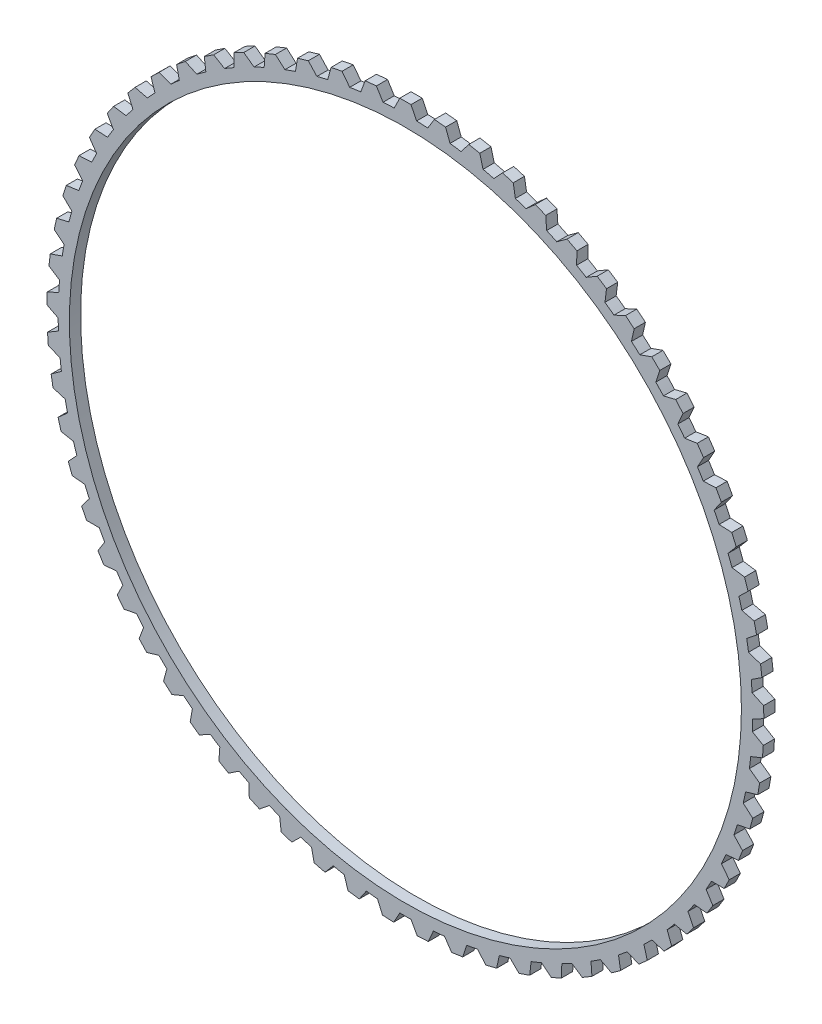
SolidWorks part; units mm, degrees
ref_plane "Front Plane" through (0, 0, 0) normal (0, 0, 1) x (1, 0, 0)
ref_plane "Top Plane" through (0, 0, 0) normal (0, 1, 0) x (1, 0, 0)
ref_plane "Right Plane" through (0, 0, 0) normal (1, 0, 0) x (0, 0, -1)
sketch "Sketch1" plane through (0, 0, 0) normal (0, 0, 1) x (1, 0, 0)
  line L0 (0, 320) -> (0, 310) construction
  line L1 (-5, 320) -> (5, 320)
  line L2 (-5, 320) -> (-9.9987, 309.8387)
  line L3 (5, 320) -> (9.9987, 309.8387)
  line L4 (25.9078, 318.9887) -> (35.8611, 318.0236)
  line L5 (35.8611, 318.0236) -> (39.8558, 307.4273)
  line L6 (25.9078, 318.9887) -> (19.9517, 309.3573)
  line L7 (56.5737, 314.9991) -> (66.3874, 313.0778)
  line L8 (66.3874, 313.0778) -> (69.3407, 302.1454)
  line L9 (56.5737, 314.9991) -> (49.7159, 305.9875)
  line L10 (86.7114, 308.0684) -> (96.2938, 305.2089)
  line L11 (96.2938, 305.2089) -> (98.1783, 294.0426)
  line L12 (86.7114, 308.0684) -> (79.0158, 299.7607)
  line L13 (116.0395, 298.2614) -> (125.3012, 294.4904)
  line L14 (125.3012, 294.4904) -> (126.0991, 283.1943)
  line L15 (116.0395, 298.2614) -> (107.578, 290.7352)
  line L16 (144.2841, 285.6695) -> (153.1387, 281.0223)
  line L17 (153.1387, 281.0223) -> (152.8426, 269.7019)
  line L18 (144.2841, 285.6695) -> (135.1358, 278.9952)
  line L19 (171.1817, 270.4105) -> (179.5464, 264.9304)
  line L20 (179.5464, 264.9304) -> (178.1591, 253.6914)
  line L21 (171.1817, 270.4105) -> (161.4319, 264.6502)
  line L22 (196.4809, 252.6267) -> (204.2776, 246.3649)
  line L23 (204.2776, 246.3649) -> (201.8121, 235.3123)
  line L24 (196.4809, 252.6267) -> (186.2207, 247.8343)
  line L25 (219.9456, 232.4842) -> (227.1016, 225.4991)
  line L26 (227.1016, 225.4991) -> (223.5809, 214.7361)
  line L27 (219.9456, 232.4842) -> (209.2708, 228.7045)
  line L28 (241.3568, 210.1711) -> (247.8052, 202.5279)
  line L29 (247.8052, 202.5279) -> (243.2622, 192.1549)
  line L30 (241.3568, 210.1711) -> (230.367, 207.4392)
  line L31 (260.5145, 185.8956) -> (266.1952, 177.6658)
  line L32 (266.1952, 177.6658) -> (260.6722, 167.7797)
  line L33 (260.5145, 185.8956) -> (249.3124, 184.2372)
  line L34 (277.2399, 159.8845) -> (282.0997, 151.1449)
  line L35 (282.0997, 151.1449) -> (275.6483, 141.8379)
  line L36 (277.2399, 159.8845) -> (265.9299, 159.315)
  line L37 (291.3767, 132.3806) -> (295.3703, 123.2127)
  line L38 (295.3703, 123.2127) -> (288.0508, 114.5719)
  line L39 (291.3767, 132.3806) -> (280.0646, 132.9053)
  line L40 (302.793, 103.6407) -> (305.8832, 94.1302)
  line L41 (305.8832, 94.1302) -> (297.7639, 86.2361)
  line L42 (302.793, 103.6407) -> (291.5844, 105.2548)
  line L43 (311.3822, 73.9331) -> (313.5401, 64.1687)
  line L44 (313.5401, 64.1687) -> (304.6968, 57.0952)
  line L45 (311.3822, 73.9331) -> (300.3817, 76.6214)
  line L46 (317.0642, 43.5353) -> (318.2695, 33.6082)
  line L47 (318.2695, 33.6082) -> (308.7848, 27.4211)
  line L48 (317.0642, 43.5353) -> (306.3744, 47.2727)
  line L49 (319.7857, 12.7309) -> (320.0274, 2.7339)
  line L50 (320.0274, 2.7339) -> (309.9898, -2.5089)
  line L51 (319.7857, 12.7309) -> (309.5066, 17.4826)
  line L52 (319.5216, -18.1923) -> (318.7972, -28.166)
  line L53 (318.7972, -28.166) -> (308.3006, -32.4155)
  line L54 (319.5216, -18.1923) -> (309.7491, -12.4707)
  line L55 (316.2741, -48.9456) -> (314.5906, -58.8029)
  line L56 (314.5906, -58.8029) -> (303.7327, -62.0195)
  line L57 (316.2741, -48.9456) -> (307.0994, -42.3075)
  line L58 (310.0737, -79.242) -> (307.4466, -88.8907)
  line L59 (307.4466, -88.8907) -> (296.3291, -91.0444)
  line L60 (310.0737, -79.242) -> (301.5825, -71.7494)
  line L61 (300.9782, -108.7985) -> (297.4322, -118.1486)
  line L62 (297.4322, -118.1486) -> (286.1586, -119.2193)
  line L63 (300.9782, -108.7985) -> (293.2498, -100.5214)
  line L64 (289.0726, -137.3392) -> (284.6407, -146.3034)
  line L65 (284.6407, -146.3034) -> (273.3164, -146.281)
  line L66 (289.0726, -137.3392) -> (282.1791, -128.3548)
  line L67 (274.4679, -164.5975) -> (269.1915, -173.0922)
  line L68 (269.1915, -173.0922) -> (257.9223, -171.9769)
  line L69 (274.4679, -164.5975) -> (268.4738, -154.9898)
  line L70 (257.3007, -190.3191) -> (251.229, -198.2649)
  line L71 (251.229, -198.2649) -> (240.1201, -196.0672)
  line L72 (257.3007, -190.3191) -> (252.2618, -180.1777)
  line L73 (237.7311, -214.2637) -> (230.9209, -221.5864)
  line L74 (230.9209, -221.5864) -> (220.0759, -218.3268)
  line L75 (237.7311, -214.2637) -> (233.6945, -203.6833)
  line L76 (215.9418, -236.2078) -> (208.4567, -242.8391)
  line L77 (208.4567, -242.8391) -> (197.9769, -238.548)
  line L78 (215.9418, -236.2078) -> (212.9452, -225.2872)
  line L79 (192.1364, -255.9465) -> (184.0462, -261.8244)
  line L80 (184.0462, -261.8244) -> (174.0295, -256.5419)
  line L81 (192.1364, -255.9465) -> (190.2077, -244.7877)
  line L82 (166.537, -273.2955) -> (157.9173, -278.3651)
  line L83 (157.9173, -278.3651) -> (148.4572, -272.1405)
  line L84 (166.537, -273.2955) -> (165.6944, -262.0026)
  line L85 (139.3827, -288.0928) -> (130.314, -292.3068)
  line L86 (130.314, -292.3068) -> (121.4988, -285.1982)
  line L87 (139.3827, -288.0928) -> (139.6339, -276.7713)
  line L88 (110.9271, -300.2002) -> (101.494, -303.5193)
  line L89 (101.494, -303.5193) -> (93.406, -295.5932)
  line L90 (110.9271, -300.2002) -> (112.2698, -288.9559)
  line L91 (81.4357, -309.5048) -> (71.7263, -311.898)
  line L92 (71.7263, -311.898) -> (64.4411, -303.2282)
  line L93 (81.4357, -309.5048) -> (83.8574, -298.4425)
  line L94 (51.184, -315.9196) -> (41.289, -317.3645)
  line L95 (41.289, -317.3645) -> (34.8745, -308.0321)
  line L96 (51.184, -315.9196) -> (54.6621, -305.1427)
  line L97 (20.4544, -319.3847) -> (10.4661, -319.8679)
  line L98 (10.4661, -319.8679) -> (4.9823, -309.96)
  line L99 (20.4544, -319.3847) -> (24.9564, -308.9938)
  line L100 (-10.4661, -319.8679) -> (-20.4544, -319.3847)
  line L101 (-20.4544, -319.3847) -> (-24.9564, -308.9938)
  line L102 (-10.4661, -319.8679) -> (-4.9823, -309.96)
  line L103 (-41.289, -317.3645) -> (-51.184, -315.9196)
  line L104 (-51.184, -315.9196) -> (-54.6621, -305.1427)
  line L105 (-41.289, -317.3645) -> (-34.8745, -308.0321)
  line L106 (-71.7263, -311.898) -> (-81.4357, -309.5048)
  line L107 (-81.4357, -309.5048) -> (-83.8574, -298.4425)
  line L108 (-71.7263, -311.898) -> (-64.4411, -303.2282)
  line L109 (-101.494, -303.5193) -> (-110.9271, -300.2002)
  line L110 (-110.9271, -300.2002) -> (-112.2698, -288.9559)
  line L111 (-101.494, -303.5193) -> (-93.406, -295.5932)
  line L112 (-130.314, -292.3068) -> (-139.3827, -288.0928)
  line L113 (-139.3827, -288.0928) -> (-139.6339, -276.7713)
  line L114 (-130.314, -292.3068) -> (-121.4988, -285.1982)
  line L115 (-157.9173, -278.3651) -> (-166.537, -273.2955)
  line L116 (-166.537, -273.2955) -> (-165.6944, -262.0026)
  line L117 (-157.9173, -278.3651) -> (-148.4572, -272.1405)
  line L118 (-184.0462, -261.8244) -> (-192.1364, -255.9465)
  line L119 (-192.1364, -255.9465) -> (-190.2077, -244.7877)
  line L120 (-184.0462, -261.8244) -> (-174.0295, -256.5419)
  line L121 (-208.4567, -242.8391) -> (-215.9418, -236.2078)
  line L122 (-215.9418, -236.2078) -> (-212.9452, -225.2872)
  line L123 (-208.4567, -242.8391) -> (-197.9769, -238.548)
  line L124 (-230.9209, -221.5864) -> (-237.7311, -214.2637)
  line L125 (-237.7311, -214.2637) -> (-233.6945, -203.6833)
  line L126 (-230.9209, -221.5864) -> (-220.0759, -218.3268)
  line L127 (-251.229, -198.2649) -> (-257.3007, -190.3191)
  line L128 (-257.3007, -190.3191) -> (-252.2618, -180.1777)
  line L129 (-251.229, -198.2649) -> (-240.1201, -196.0672)
  line L130 (-269.1915, -173.0922) -> (-274.4679, -164.5975)
  line L131 (-274.4679, -164.5975) -> (-268.4738, -154.9898)
  line L132 (-269.1915, -173.0922) -> (-257.9223, -171.9769)
  line L133 (-284.6407, -146.3034) -> (-289.0726, -137.3392)
  line L134 (-289.0726, -137.3392) -> (-282.1791, -128.3548)
  line L135 (-284.6407, -146.3034) -> (-273.3164, -146.281)
  line L136 (-297.4322, -118.1486) -> (-300.9782, -108.7985)
  line L137 (-300.9782, -108.7985) -> (-293.2498, -100.5214)
  line L138 (-297.4322, -118.1486) -> (-286.1586, -119.2193)
  line L139 (-307.4466, -88.8907) -> (-310.0737, -79.242)
  line L140 (-310.0737, -79.242) -> (-301.5825, -71.7494)
  line L141 (-307.4466, -88.8907) -> (-296.3291, -91.0444)
  line L142 (-314.5906, -58.8029) -> (-316.2741, -48.9456)
  line L143 (-316.2741, -48.9456) -> (-307.0994, -42.3075)
  line L144 (-314.5906, -58.8029) -> (-303.7327, -62.0195)
  line L145 (-318.7972, -28.166) -> (-319.5216, -18.1923)
  line L146 (-319.5216, -18.1923) -> (-309.7491, -12.4707)
  line L147 (-318.7972, -28.166) -> (-308.3006, -32.4155)
  line L148 (-320.0274, 2.7339) -> (-319.7857, 12.7309)
  line L149 (-319.7857, 12.7309) -> (-309.5066, 17.4826)
  line L150 (-320.0274, 2.7339) -> (-309.9898, -2.5089)
  line L151 (-318.2695, 33.6082) -> (-317.0642, 43.5353)
  line L152 (-317.0642, 43.5353) -> (-306.3744, 47.2727)
  line L153 (-318.2695, 33.6082) -> (-308.7848, 27.4211)
  line L154 (-313.5401, 64.1687) -> (-311.3822, 73.9331)
  line L155 (-311.3822, 73.9331) -> (-300.3817, 76.6214)
  line L156 (-313.5401, 64.1687) -> (-304.6968, 57.0952)
  line L157 (-305.8832, 94.1302) -> (-302.793, 103.6407)
  line L158 (-302.793, 103.6407) -> (-291.5844, 105.2548)
  line L159 (-305.8832, 94.1302) -> (-297.7639, 86.2361)
  line L160 (-295.3703, 123.2127) -> (-291.3767, 132.3806)
  line L161 (-291.3767, 132.3806) -> (-280.0646, 132.9053)
  line L162 (-295.3703, 123.2127) -> (-288.0508, 114.5719)
  line L163 (-282.0997, 151.1449) -> (-277.2399, 159.8845)
  line L164 (-277.2399, 159.8845) -> (-265.9299, 159.315)
  line L165 (-282.0997, 151.1449) -> (-275.6483, 141.8379)
  line L166 (-266.1952, 177.6658) -> (-260.5145, 185.8956)
  line L167 (-260.5145, 185.8956) -> (-249.3124, 184.2372)
  line L168 (-266.1952, 177.6658) -> (-260.6722, 167.7797)
  line L169 (-247.8052, 202.5279) -> (-241.3568, 210.1711)
  line L170 (-241.3568, 210.1711) -> (-230.367, 207.4392)
  line L171 (-247.8052, 202.5279) -> (-243.2622, 192.1549)
  line L172 (-227.1016, 225.4991) -> (-219.9456, 232.4842)
  line L173 (-219.9456, 232.4842) -> (-209.2708, 228.7045)
  line L174 (-227.1016, 225.4991) -> (-223.5809, 214.7361)
  line L175 (-204.2776, 246.3649) -> (-196.4809, 252.6267)
  line L176 (-196.4809, 252.6267) -> (-186.2207, 247.8343)
  line L177 (-204.2776, 246.3649) -> (-201.8121, 235.3123)
  line L178 (-179.5464, 264.9304) -> (-171.1817, 270.4105)
  line L179 (-171.1817, 270.4105) -> (-161.4319, 264.6502)
  line L180 (-179.5464, 264.9304) -> (-178.1591, 253.6914)
  line L181 (-153.1387, 281.0223) -> (-144.2841, 285.6695)
  line L182 (-144.2841, 285.6695) -> (-135.1358, 278.9952)
  line L183 (-153.1387, 281.0223) -> (-152.8426, 269.7019)
  line L184 (-125.3012, 294.4904) -> (-116.0395, 298.2614)
  line L185 (-116.0395, 298.2614) -> (-107.578, 290.7352)
  line L186 (-125.3012, 294.4904) -> (-126.0991, 283.1943)
  line L187 (-96.2938, 305.2089) -> (-86.7114, 308.0684)
  line L188 (-86.7114, 308.0684) -> (-79.0158, 299.7607)
  line L189 (-96.2938, 305.2089) -> (-98.1783, 294.0426)
  line L190 (-66.3874, 313.0778) -> (-56.5737, 314.9991)
  line L191 (-56.5737, 314.9991) -> (-49.7159, 305.9875)
  line L192 (-66.3874, 313.0778) -> (-69.3407, 302.1454)
  line L193 (-35.8611, 318.0236) -> (-25.9078, 318.9887)
  line L194 (-25.9078, 318.9887) -> (-19.9517, 309.3573)
  line L195 (-35.8611, 318.0236) -> (-39.8558, 307.4273)
  arc A0 (-98.1783, 294.0426) -> (-107.578, 290.7352) centre (0, 0) ccw
  arc A2 (-126.0991, 283.1943) -> (-135.1358, 278.9952) centre (0, 0) ccw
  arc A3 (-152.8426, 269.7019) -> (-161.4319, 264.6502) centre (0, 0) ccw
  arc A4 (-178.1591, 253.6914) -> (-186.2207, 247.8343) centre (0, 0) ccw
  arc A5 (-201.8121, 235.3123) -> (-209.2708, 228.7045) centre (0, 0) ccw
  arc A6 (-223.5809, 214.7361) -> (-230.367, 207.4392) centre (0, 0) ccw
  arc A7 (-243.2622, 192.1549) -> (-249.3124, 184.2372) centre (0, 0) ccw
  arc A8 (-69.3407, 302.1454) -> (-79.0158, 299.7607) centre (0, 0) ccw
  arc A9 (-260.6722, 167.7797) -> (-265.9299, 159.315) centre (0, 0) ccw
  arc A10 (-275.6483, 141.8379) -> (-280.0646, 132.9053) centre (0, 0) ccw
  arc A11 (-288.0508, 114.5719) -> (-291.5844, 105.2548) centre (0, 0) ccw
  arc A12 (-297.7639, 86.2361) -> (-300.3817, 76.6214) centre (0, 0) ccw
  arc A13 (-304.6968, 57.0952) -> (-306.3744, 47.2727) centre (0, 0) ccw
  arc A14 (-308.7848, 27.4211) -> (-309.5066, 17.4826) centre (0, 0) ccw
  arc A15 (-309.9898, -2.5089) -> (-309.7491, -12.4707) centre (0, 0) ccw
  arc A16 (-308.3006, -32.4155) -> (-307.0994, -42.3075) centre (0, 0) ccw
  arc A17 (-303.7327, -62.0195) -> (-301.5825, -71.7494) centre (0, 0) ccw
  arc A18 (-296.3291, -91.0444) -> (-293.2498, -100.5214) centre (0, 0) ccw
  arc A19 (-286.1586, -119.2193) -> (-282.1791, -128.3548) centre (0, 0) ccw
  arc A20 (-273.3164, -146.281) -> (-268.4738, -154.9898) centre (0, 0) ccw
  arc A21 (-257.9223, -171.9769) -> (-252.2618, -180.1777) centre (0, 0) ccw
  arc A22 (-240.1201, -196.0672) -> (-233.6945, -203.6833) centre (0, 0) ccw
  arc A23 (-220.0759, -218.3268) -> (-212.9452, -225.2872) centre (0, 0) ccw
  arc A24 (-197.9769, -238.548) -> (-190.2077, -244.7877) centre (0, 0) ccw
  arc A25 (-174.0295, -256.5419) -> (-165.6944, -262.0026) centre (0, 0) ccw
  arc A26 (-148.4572, -272.1405) -> (-139.6339, -276.7713) centre (0, 0) ccw
  arc A27 (-121.4988, -285.1982) -> (-112.2698, -288.9559) centre (0, 0) ccw
  arc A28 (-93.406, -295.5932) -> (-83.8574, -298.4425) centre (0, 0) ccw
  arc A29 (-64.4411, -303.2282) -> (-54.6621, -305.1427) centre (0, 0) ccw
  arc A30 (-34.8745, -308.0321) -> (-24.9564, -308.9938) centre (0, 0) ccw
  arc A31 (-4.9823, -309.96) -> (4.9823, -309.96) centre (0, 0) ccw
  arc A32 (24.9564, -308.9938) -> (34.8745, -308.0321) centre (0, 0) ccw
  arc A33 (54.6621, -305.1427) -> (64.4411, -303.2282) centre (0, 0) ccw
  arc A34 (83.8574, -298.4425) -> (93.406, -295.5932) centre (0, 0) ccw
  arc A35 (112.2698, -288.9559) -> (121.4988, -285.1982) centre (0, 0) ccw
  arc A36 (139.6339, -276.7713) -> (148.4572, -272.1405) centre (0, 0) ccw
  arc A37 (165.6944, -262.0026) -> (174.0295, -256.5419) centre (0, 0) ccw
  arc A38 (190.2077, -244.7877) -> (197.9769, -238.548) centre (0, 0) ccw
  arc A39 (212.9452, -225.2872) -> (220.0759, -218.3268) centre (0, 0) ccw
  arc A40 (233.6945, -203.6833) -> (240.1201, -196.0672) centre (0, 0) ccw
  arc A41 (252.2618, -180.1777) -> (257.9223, -171.9769) centre (0, 0) ccw
  arc A42 (268.4738, -154.9898) -> (273.3164, -146.281) centre (0, 0) ccw
  arc A43 (293.2498, -100.5214) -> (296.3291, -91.0444) centre (0, 0) ccw
  arc A44 (282.1791, -128.3548) -> (286.1586, -119.2193) centre (0, 0) ccw
  arc A45 (301.5825, -71.7494) -> (303.7327, -62.0195) centre (0, 0) ccw
  arc A46 (307.0994, -42.3075) -> (308.3006, -32.4155) centre (0, 0) ccw
  arc A47 (309.7491, -12.4707) -> (309.9898, -2.5089) centre (0, 0) ccw
  arc A48 (309.5066, 17.4826) -> (308.7848, 27.4211) centre (0, 0) ccw
  arc A49 (306.3744, 47.2727) -> (304.6968, 57.0952) centre (0, 0) ccw
  arc A50 (300.3817, 76.6214) -> (297.7639, 86.2361) centre (0, 0) ccw
  arc A51 (291.5844, 105.2548) -> (288.0508, 114.5719) centre (0, 0) ccw
  arc A52 (280.0646, 132.9053) -> (275.6483, 141.8379) centre (0, 0) ccw
  arc A53 (265.9299, 159.315) -> (260.6722, 167.7797) centre (0, 0) ccw
  arc A54 (249.3124, 184.2372) -> (243.2622, 192.1549) centre (0, 0) ccw
  arc A55 (230.367, 207.4392) -> (223.5809, 214.7361) centre (0, 0) ccw
  arc A56 (209.2708, 228.7045) -> (201.8121, 235.3123) centre (0, 0) ccw
  arc A57 (186.2207, 247.8343) -> (178.1591, 253.6914) centre (0, 0) ccw
  arc A58 (161.4319, 264.6502) -> (152.8426, 269.7019) centre (0, 0) ccw
  arc A59 (135.1358, 278.9952) -> (126.0991, 283.1943) centre (0, 0) ccw
  arc A60 (107.578, 290.7352) -> (98.1783, 294.0426) centre (0, 0) ccw
  arc A61 (79.0158, 299.7607) -> (69.3407, 302.1454) centre (0, 0) ccw
  arc A62 (49.7159, 305.9875) -> (39.8558, 307.4273) centre (0, 0) ccw
  arc A63 (19.9517, 309.3573) -> (9.9987, 309.8387) centre (0, 0) ccw
  arc A64 (-9.9987, 309.8387) -> (-19.9517, 309.3573) centre (0, 0) ccw
  arc A65 (-39.8558, 307.4273) -> (-49.7159, 305.9875) centre (0, 0) ccw
  circle A66 centre (0, 0) radius 300
  point P3 (9.827, 320)
  point P5 (0, 310)
  point P6 (0, 310)
  point P10 (-9.9987, 309.8387)
  point P11 (9.9987, 309.8387)
  point P12 (0, 0)
  dimension "D1" = 620
  dimension "D4" = 10
  dimension "D3" = 10
  dimension "D2" = 10
  dimension "D5" = 10
  dimension "D6" = 65
extrude "Boss-Extrude4" add sketch "Sketch1" along normal blind 10
